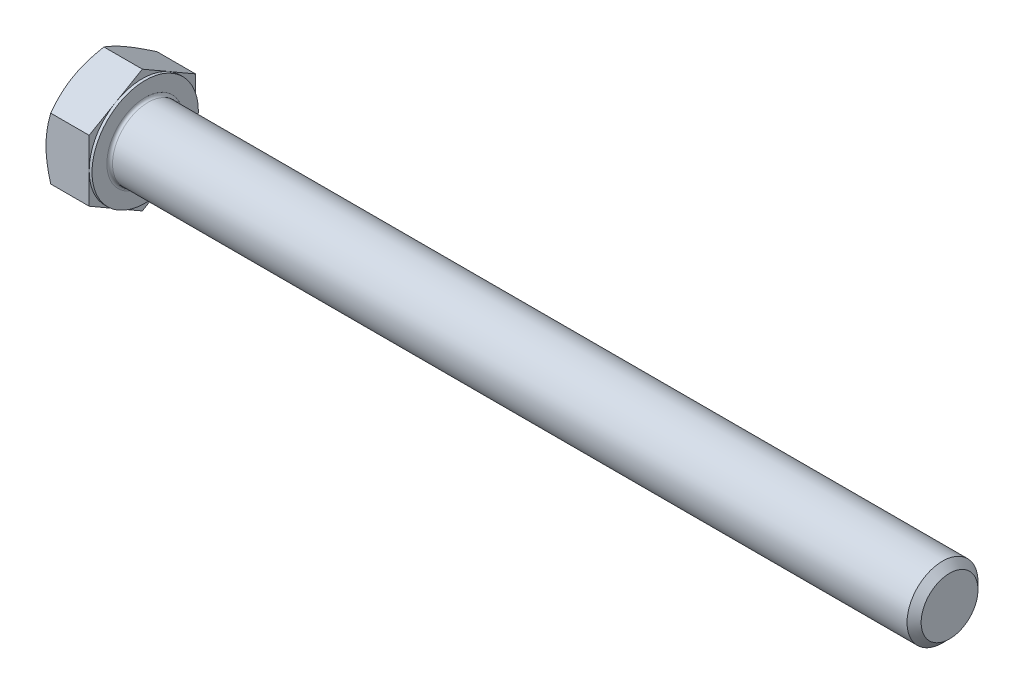
SolidWorks part; units mm, degrees
extrude "BaseHead" add sketch "Sketch1" along normal blind 6.1722
sketch "Sketch1" plane through (0, 0, 0) normal (1, 0, 0) x (0, 0, -1)
  line L0 (7.1374, 4.1208) -> (7.1374, -4.1208)
  line L1 (-7.1374, 4.1208) -> (-7.1374, -4.1208)
  line L2 (7.1374, -4.1208) -> (0, -8.2416)
  line L3 (0, -8.2416) -> (-7.1374, -4.1208)
  line L4 (7.1374, 4.1208) -> (0, 8.2416)
  line L5 (0, 8.2416) -> (-7.1374, 4.1208)
  dimension "Width_flats" = 14.2748
  dimension "D2" = 120
  dimension "D3" = 7.1374
  dimension "D4" = 7.1374
  dimension "D5" = 7.1374
revolve "HeadChamfer" cut sketch "Sketch3" angle 360 about L6
sketch "Sketch3" plane through (0, 0, 0) normal (0, 0, 1) x (1, 0, 0)
  line L0 (0, 7.1374) -> (4.3037, 14.5916)
  line L1 (0, 8.2416) -> (0, 4.1208) construction
  line L2 (4.3037, 14.5916) -> (4.3037, 20.9416)
  line L3 (4.3037, 20.9416) -> (-12.7, 20.9416)
  line L4 (-12.7, 20.9416) -> (-12.7, 7.1374)
  line L5 (-12.7, 7.1374) -> (0, 7.1374)
  line L6 (0, 0) -> (99.06, 0) construction
  line L7 (6.1722, 8.2416) -> (0, 8.2416) construction
  dimension "D1" = 7.1374
  dimension "D2" = 6.35
  dimension "D3" = 12.7
  dimension "D4" = 6.35
  dimension "Head_ch_ang" = 30
ref_plane "Plane1" through (0, 0, 0) normal (0, 0, 1) x (1, 0, 0)
ref_plane "Plane2" through (0, 0, 0) normal (0, 1, 0) x (1, 0, 0)
ref_plane "Plane3" through (0, 0, 0) normal (1, 0, 0) x (0, 0, -1)
sketch "BodySke" plane through (0, 0, 0) normal (0, 0, 1) x (1, 0, 0)
  line L0 (0, 4.1208) -> (0, -4.1208) construction
  line L1 (0, 0) -> (114.1222, 0)
  line L2 (0, 0) -> (0, 4.7625)
  line L3 (0, 4.7625) -> (113.176, 4.7625)
  line L4 (114.1222, 0) -> (114.1222, 3.8163)
  line L5 (6.1722, 8.2416) -> (6.1722, 4.1208) construction
  line L6 (114.1222, 3.8163) -> (113.176, 4.7625)
  line L7 (0, 0) -> (96.52, 0) construction
  line L8 (114.1222, -3.8163) -> (113.176, -4.7625) construction
  line L9 (0, -4.7625) -> (113.176, -4.7625) construction
  line L10 (7.7597, 15.24) -> (7.7597, -1.27) construction
  line L11 (88.7222, 15.24) -> (88.7222, -1.27) construction
  line L12 (6.1722, 4.1208) -> (6.1722, -4.1208) construction
  dimension "Diameter" = 9.525
revolve "BaseBody" add sketch "BodySke" angle 360 about L7
cosmetic thread "ThreadCosmetic"
sketch "Sketch4" plane through (0, 0, 0) normal (0, 0, 1) x (1, 0, 0)
  line L1 (6.1722, 8.2416) -> (6.1722, 4.1208) construction
  line L2 (6.1722, 7.1374) -> (5.7912, 7.1374)
  line L3 (6.1722, 7.1374) -> (6.1722, 33.6416)
  line L4 (6.1722, 33.6416) -> (5.7912, 33.6416)
  line L5 (0, 0) -> (95.25, 0) construction
  line L6 (0, 0) -> (96.52, 0) construction
  line L7 (5.7912, 7.1374) -> (5.7912, 33.6416)
  line L8 (6.1722, 8.2416) -> (0.6375, 8.2416) construction
  dimension "D1" = 7.1374
  dimension "D2" = 25.4
revolve "BearingFace" cut sketch "Sketch4" angle 360 about L5
fillet "HeadFillet" radius 0.381 1 edges at (6.1722, 0, -4.7625)
sketch "ThdSchSke" plane through (0, 0, 0) normal (0, 0, 1) x (1, 0, 0)
  line L0 (88.7222, -3.8163) -> (88.0597, -4.7625)
  line L1 (88.7222, -3.8163) -> (89.3847, -4.7625)
  line L2 (89.3847, -4.7625) -> (89.3847, -5.9531)
  line L3 (-3.175, 0) -> (5.1513, 0) construction
  line L5 (89.3847, -5.9531) -> (88.0597, -5.9531)
  line L6 (88.0597, -5.9531) -> (88.0597, -4.7625)
  dimension "Thread_minor" = 7.6327
  dimension "Diameter" = 9.525
  dimension "Start" = 88.7222
revolve "ThreadSchematic" [suppressed] cut sketch "ThdSchSke" angle 360 about L3
pattern_linear "ThdSchPat" [suppressed]
equation "\"D3@Sketch1\" = \"Width_flats@Sketch1\" / 2"
equation "\"D4@Sketch1\" = \"D3@Sketch1\""
equation "\"D5@Sketch1\" = \"D4@Sketch1\""
equation "\"Thread_minor@ThreadCosmetic\" = \"Minor_dia@BodySke\""
equation "\"D1@Sketch3\" = \"Width_flats@Sketch1\" / 2"
equation "\"D1@Sketch4\" = \"Width_flats@Sketch1\" / 2"
equation "\"Thread_length@ThreadCosmetic\" = ((sgn( (\"Length@BodySke\" - \"Advance@BodySke\" ) - \"Thread_nom@BodySke\" )-1)*( (\"Length@BodySke\" - \"Advance@BodySke\" ) - \"Thread_nom@BodySke\" ))/-2+ \"Thread_nom@BodySke\""
equation "\"Thread_minor@ThdSchSke\" = \"Minor_dia@BodySke\""
equation "\"Diameter@ThdSchSke\" = \"Diameter@BodySke\""
equation "\"Overcut@ThdSchSke\" = \"Diameter@BodySke\" * 1.25"
equation "\"Start@ThdSchSke\" = \"Head_ht@BaseHead\" + \"Length@BodySke\" - \"Thread_length@ThreadCosmetic\"  '---Non-countersunk---"
equation "\"Num_threads@ThdSchPat\" = int( \"Thread_length@ThreadCosmetic\" / \"Advance@BodySke\" + 0.999 )  + 1"
equation "\"Advance@ThdSchPat\" = \"Thread_length@ThreadCosmetic\" /  (\"Num_threads@ThdSchPat\" - 1) 'relax it"
equation "\"Num_threads@ThdSchPat\" = \"Num_threads@ThdSchPat\" - sgn( \"Num_threads@ThdSchPat\" - 1) '---chamfered tips only---"
